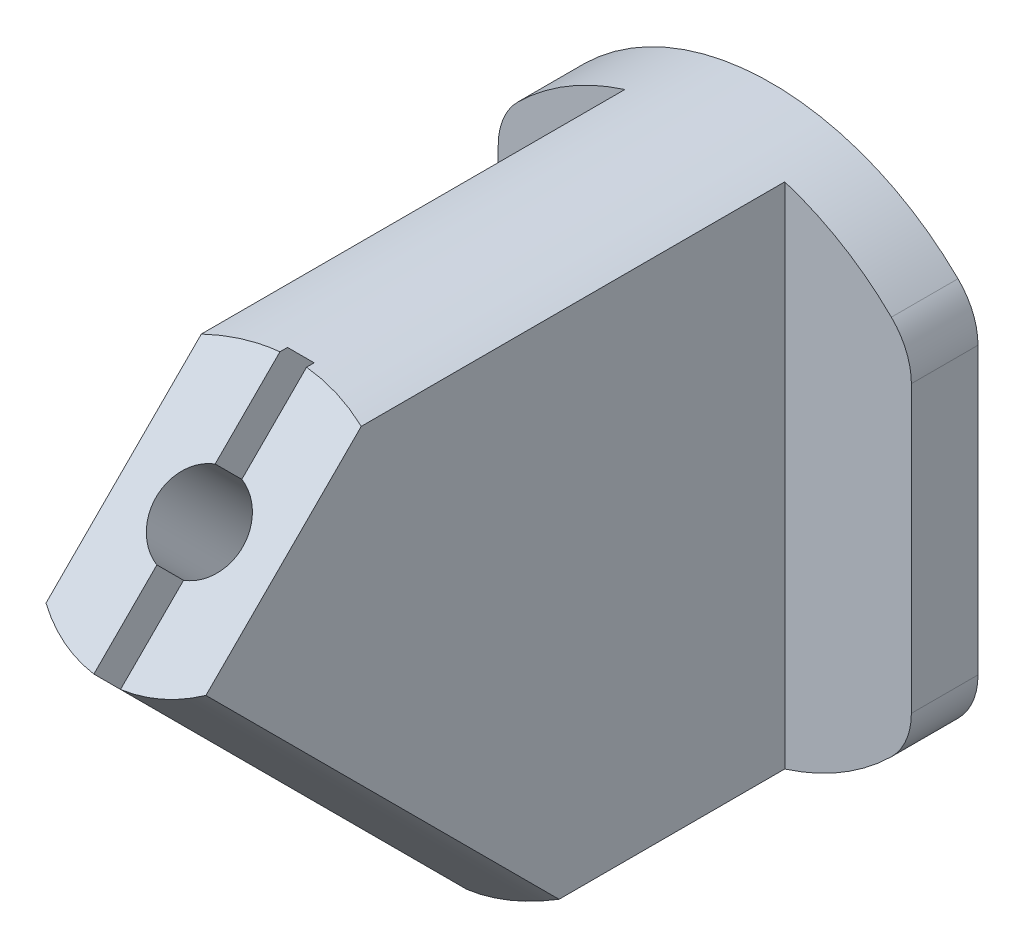
SolidWorks part; units mm, degrees
ref_plane "Front Plane" through (0, 0, 0) normal (0, 0, 1) x (1, 0, 0)
ref_plane "Top Plane" through (0, 0, 0) normal (0, 1, 0) x (1, 0, 0)
ref_plane "Right Plane" through (0, 0, 0) normal (1, 0, 0) x (0, 0, -1)
sketch "Sketch1" plane through (0, 0, 0) normal (0, 0, 1) x (1, 0, 0)
  line L0 (-15.5, 10.7121) -> (-15.5, -10.7121)
  line L1 (15.5, 10.7121) -> (15.5, -10.7121)
  line L2 (11.1369, 11.1369) -> (0, 0) construction
  line L3 (0, 0) -> (13.989, 0) construction
  arc A0 (-14, -14.2829) -> (14, -14.2829) centre (0, 0) ccw
  circle A1 centre (11.1369, 11.1369) radius 4 construction
  arc A2 (14, 14.2829) -> (-14, 14.2829) centre (0, 0) ccw
  arc A3 (-15.5, 10.7121) -> (-14, 14.2829) centre (-10.5, 10.7121) cw
  arc A4 (-14, -14.2829) -> (-15.5, -10.7121) centre (-10.5, -10.7121) cw
  arc A5 (15.5, -10.7121) -> (14, -14.2829) centre (10.5, -10.7121) cw
  arc A6 (15.5, 10.7121) -> (14, 14.2829) centre (10.5, 10.7121) ccw
  point P17 (15.5, 12.6392)
  dimension "D1" = 40
  dimension "D3" = 8
  dimension "D7" = 5
  dimension "D2" = 15.5
  dimension "D4" = 15.75
  dimension "D5" = 45
  dimension "D6" = 15.5
extrude "Boss-Extrude1" add sketch "Sketch1" along normal blind 50
sketch "Sketch2" plane through (0, 0, 0) normal (1, 0, 0) x (0, 0, -1)
  line L0 (0, 270) -> (-300, 270) construction
  line L1 (-300, 270) -> (-300, 0) construction
  line L2 (-300, 270) -> (0, -30) construction
  point P3 (0, 0)
  dimension "D1" = 270
  dimension "D2" = 300
  dimension "D3" = 45
sketch "Sketch3" plane through (0, 0, 0) normal (0, 1, 0) x (1, 0, 0)
  line L0 (-18.0676, -5) -> (-6, -5)
  line L1 (-6, -5) -> (-6, -53.7568)
  line L2 (-6, -53.7568) -> (6, -53.7568)
  line L3 (6, -53.7568) -> (6, -5)
  line L4 (6, -5) -> (19.8488, -5)
  line L5 (0, -300) -> (0, 0) construction
  line L6 (0, 17.8407) -> (0, -62.9568) construction
  line L7 (14, 0) -> (-14, 0) construction
  dimension "D1" = 6
  dimension "D2" = 5
extrude "Cut-Extrude2" cut sketch "Sketch3" against normal through all and the other way through all flip side to cut
sketch "Sketch4" plane through (-6, 0, 0) normal (-1, 0, 0) x (0, 0, 1)
  line L0 (54.2635, 1.5944) -> (31.5859, 24.272)
  line L1 (300, 270) -> (0, -30) construction
  dimension "D1" = 10
extrude "Cut-Extrude3" cut sketch "Sketch4" against normal through all and the other way through all flip side to cut
sketch "Sketch5" plane through (0, 27.9289, 27.9289) normal (0, 0.7071, 0.7071) x (1, 0, 0)
  line L0 (0, -21.2132) -> (0, -212.132) construction
  line L1 (0, 190.9188) -> (0, -21.2132) construction
  line L2 (-7.5145, -27.5522) -> (-7.5145, -51.5107)
  line L3 (-7.5145, -51.5107) -> (9.2939, -51.5107)
  line L4 (9.2939, -51.5107) -> (9.2939, -24.4184)
  line L5 (1, -30.9933) -> (1, -24.3055)
  line L6 (-1, -30.9933) -> (-1, -24.3055)
  line L7 (1, -18.1209) -> (1, -10.846)
  line L8 (1, -10.846) -> (-1, -10.846)
  line L9 (-1, -10.846) -> (-1, -18.1209)
  arc A0 (1, -24.3055) -> (1, -18.1209) centre (0, -21.2132) ccw
  arc A1 (-7.5145, -27.5522) -> (-1, -30.9933) centre (0, -21.2132) ccw
  arc A2 (1, -30.9933) -> (9.2939, -24.4184) centre (0, -21.2132) ccw
  arc A3 (-1, -18.1209) -> (-1, -24.3055) centre (0, -21.2132) ccw
  dimension "D1" = 6.5
  dimension "D2" = 1
  dimension "D3" = 1
  dimension "D4" = 10.3672
  dimension "D5" = 1
  dimension "D6" = 1
extrude "Cut-Extrude4" cut sketch "Sketch5" against normal through all
